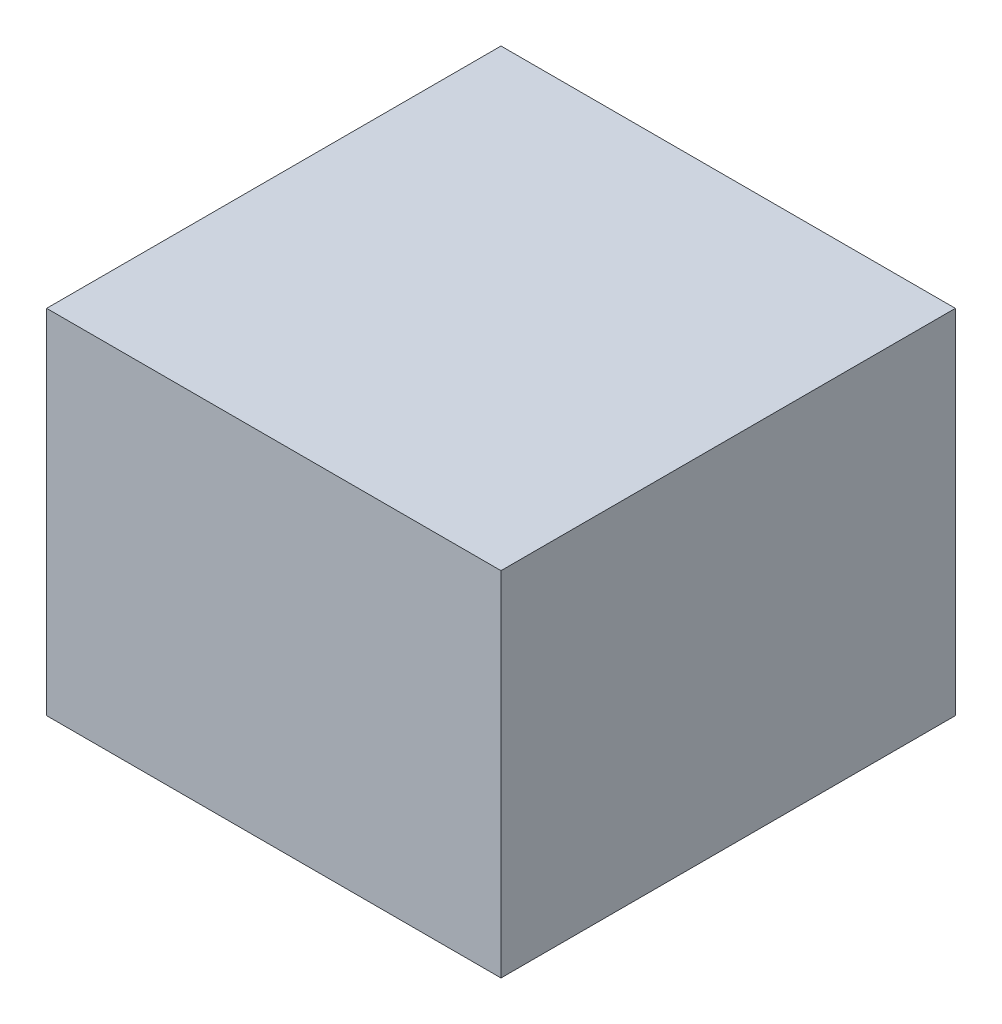
SolidWorks part; units mm, degrees
ref_plane "Front Plane" through (0, 0, 0) normal (0, 0, 1) x (1, 0, 0)
ref_plane "Top Plane" through (0, 0, 0) normal (0, 1, 0) x (1, 0, 0)
ref_plane "Right Plane" through (0, 0, 0) normal (1, 0, 0) x (0, 0, -1)
sketch "Sketch2" plane through (0, 0, 0) normal (0, 1, 0) x (1, 0, 0)
  line L1 (-16.1, 16.1) -> (16.1, 16.1)
  line L2 (-16.1, 16.1) -> (-16.1, -16.1)
  line L3 (-16.1, -16.1) -> (16.1, -16.1)
  line L4 (16.1, 16.1) -> (16.1, -16.1)
  line L5 (-16.1, 16.1) -> (16.1, -16.1) construction
  line L6 (-16.1, -16.1) -> (16.1, 16.1) construction
  point P0 (0, 0)
  dimension "D1" = 32.2
  dimension "D2" = 32.2
extrude "Boss-Extrude1" add sketch "Sketch2" along normal blind 25
